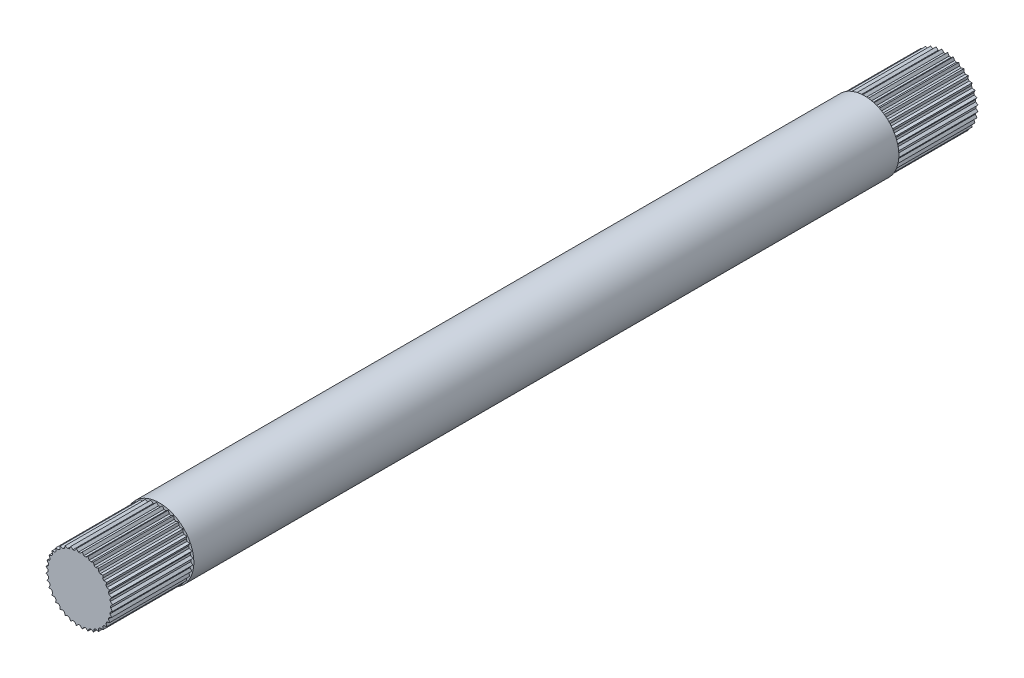
SolidWorks part; units mm, degrees
material "AISI 1015 Steel, Cold Drawn (SS)"
ref_plane "X-Y Datum" through (0, 0, 0) normal (0, 0, 1) x (1, 0, 0)
ref_plane "X-Z Datum" through (0, 0, 0) normal (0, 1, 0) x (1, 0, 0)
ref_plane "Y-Z Datum" through (0, 0, 0) normal (1, 0, 0) x (0, 0, -1)
sketch "Sketch9" plane through (0, 0, 0) normal (0, 1, 0) x (1, 0, 0)
  line L0 (16.002, 0) -> (0, 0)
  line L1 (0, 0) -> (0, -389.0916)
  line L2 (0, -389.0916) -> (-72.2493, -524.9728)
  dimension "D1" = 153.895
  dimension "D2" = 28
  dimension "D3" = 389.0916
  dimension "D5" = 16.002
sketch "Sketch5" plane through (0, 0, 0) normal (0, 1, 0) x (1, 0, 0)
  line L0 (7.9375, -262.0916) -> (7.9375, -22.1615)
  line L1 (7.9375, -22.1615) -> (9.525, -22.1615)
  line L2 (9.525, -22.1615) -> (9.525, -262.0916)
  line L3 (9.525, -262.0916) -> (7.9375, -262.0916)
  line L5 (16.002, 0) -> (0, 0) construction
  line L6 (0, 0) -> (0, -389.0916) construction
  line L7 (0, -389.0916) -> (9.525, -389.0916) construction
  line L8 (12.5602, -369.8416) -> (0, -369.8416) construction
  dimension "D1" = 1.5875
  dimension "D2" = 22.1615
  dimension "D3" = 7.9375
  dimension "D4" = 19.25
  dimension "D5" = 127
revolve "Revolve2" add sketch "Sketch5" angle 360 about L1
sketch "Sketch6" plane through (0, 0, 0) normal (0, 1, 0) x (1, 0, 0)
  circle A0 centre (0, -33.1635) radius 1.5875 construction
  circle A1 centre (0, -33.1635) radius 1.5875
sketch "Sketch7" plane through (0, 0, 0) normal (1, 0, 0) x (0, 0, -1)
  circle A2 centre (-39.196, 0) radius 1.5875
  circle A4 centre (-39.196, 0) radius 1.5875 construction
extrude "Cut-Extrude5" [suppressed] cut sketch "Sketch7" against normal through all both and the other way through all
extrude "Cut-Extrude6" [suppressed] cut sketch "Sketch6" against normal through all both and the other way through all
sketch "Sketch8" plane through (0, 0, 0) normal (0, 0, 1) x (1, 0, 0)
  line L0 (9.2357, -0.808) -> (8.6817, -0.254)
  line L1 (8.6817, -0.254) -> (8.6817, 0.254)
  line L2 (8.6817, 0.254) -> (9.2357, 0.808)
  line L3 (8.6817, 0) -> (0, 0) construction
  line L4 (8.9551, -2.3995) -> (8.5057, -1.7577)
  line L5 (8.5057, -1.7577) -> (8.5939, -1.2574)
  line L6 (8.5939, -1.2574) -> (9.2357, -0.808)
  line L7 (8.4024, -3.9181) -> (8.0713, -3.208)
  line L8 (8.0713, -3.208) -> (8.245, -2.7306)
  line L9 (8.245, -2.7306) -> (8.9551, -2.3995)
  line L10 (7.5944, -5.3176) -> (7.3916, -4.5608)
  line L11 (7.3916, -4.5608) -> (7.6456, -4.1209)
  line L12 (7.6456, -4.1209) -> (8.4024, -3.9181)
  line L13 (6.5556, -6.5556) -> (6.4873, -5.7751)
  line L14 (6.4873, -5.7751) -> (6.8138, -5.3859)
  line L15 (6.8138, -5.3859) -> (7.5944, -5.3176)
  line L16 (5.3176, -7.5944) -> (5.3859, -6.8138)
  line L17 (5.3859, -6.8138) -> (5.7751, -6.4873)
  line L18 (5.7751, -6.4873) -> (6.5556, -6.5556)
  line L19 (3.9181, -8.4024) -> (4.1209, -7.6456)
  line L20 (4.1209, -7.6456) -> (4.5608, -7.3916)
  line L21 (4.5608, -7.3916) -> (5.3176, -7.5944)
  line L22 (2.3995, -8.9551) -> (2.7306, -8.245)
  line L23 (2.7306, -8.245) -> (3.208, -8.0713)
  line L24 (3.208, -8.0713) -> (3.9181, -8.4024)
  line L25 (0.808, -9.2357) -> (1.2574, -8.5939)
  line L26 (1.2574, -8.5939) -> (1.7577, -8.5057)
  line L27 (1.7577, -8.5057) -> (2.3995, -8.9551)
  line L28 (-0.808, -9.2357) -> (-0.254, -8.6817)
  line L29 (-0.254, -8.6817) -> (0.254, -8.6817)
  line L30 (0.254, -8.6817) -> (0.808, -9.2357)
  line L31 (-2.3995, -8.9551) -> (-1.7577, -8.5057)
  line L32 (-1.7577, -8.5057) -> (-1.2574, -8.5939)
  line L33 (-1.2574, -8.5939) -> (-0.808, -9.2357)
  line L34 (-3.9181, -8.4024) -> (-3.208, -8.0713)
  line L35 (-3.208, -8.0713) -> (-2.7306, -8.245)
  line L36 (-2.7306, -8.245) -> (-2.3995, -8.9551)
  line L37 (-5.3176, -7.5944) -> (-4.5608, -7.3916)
  line L38 (-4.5608, -7.3916) -> (-4.1209, -7.6456)
  line L39 (-4.1209, -7.6456) -> (-3.9181, -8.4024)
  line L40 (-6.5556, -6.5556) -> (-5.7751, -6.4873)
  line L41 (-5.7751, -6.4873) -> (-5.3859, -6.8138)
  line L42 (-5.3859, -6.8138) -> (-5.3176, -7.5944)
  line L43 (-7.5944, -5.3176) -> (-6.8138, -5.3859)
  line L44 (-6.8138, -5.3859) -> (-6.4873, -5.7751)
  line L45 (-6.4873, -5.7751) -> (-6.5556, -6.5556)
  line L46 (-8.4024, -3.9181) -> (-7.6456, -4.1209)
  line L47 (-7.6456, -4.1209) -> (-7.3916, -4.5608)
  line L48 (-7.3916, -4.5608) -> (-7.5944, -5.3176)
  line L49 (-8.9551, -2.3995) -> (-8.245, -2.7306)
  line L50 (-8.245, -2.7306) -> (-8.0713, -3.208)
  line L51 (-8.0713, -3.208) -> (-8.4024, -3.9181)
  line L52 (-9.2357, -0.808) -> (-8.5939, -1.2574)
  line L53 (-8.5939, -1.2574) -> (-8.5057, -1.7577)
  line L54 (-8.5057, -1.7577) -> (-8.9551, -2.3995)
  line L55 (-9.2357, 0.808) -> (-8.6817, 0.254)
  line L56 (-8.6817, 0.254) -> (-8.6817, -0.254)
  line L57 (-8.6817, -0.254) -> (-9.2357, -0.808)
  line L58 (-8.9551, 2.3995) -> (-8.5057, 1.7577)
  line L59 (-8.5057, 1.7577) -> (-8.5939, 1.2574)
  line L60 (-8.5939, 1.2574) -> (-9.2357, 0.808)
  line L61 (-8.4024, 3.9181) -> (-8.0713, 3.208)
  line L62 (-8.0713, 3.208) -> (-8.245, 2.7306)
  line L63 (-8.245, 2.7306) -> (-8.9551, 2.3995)
  line L64 (-7.5944, 5.3176) -> (-7.3916, 4.5608)
  line L65 (-7.3916, 4.5608) -> (-7.6456, 4.1209)
  line L66 (-7.6456, 4.1209) -> (-8.4024, 3.9181)
  line L67 (-6.5556, 6.5556) -> (-6.4873, 5.7751)
  line L68 (-6.4873, 5.7751) -> (-6.8138, 5.3859)
  line L69 (-6.8138, 5.3859) -> (-7.5944, 5.3176)
  line L70 (-5.3176, 7.5944) -> (-5.3859, 6.8138)
  line L71 (-5.3859, 6.8138) -> (-5.7751, 6.4873)
  line L72 (-5.7751, 6.4873) -> (-6.5556, 6.5556)
  line L73 (-3.9181, 8.4024) -> (-4.1209, 7.6456)
  line L74 (-4.1209, 7.6456) -> (-4.5608, 7.3916)
  line L75 (-4.5608, 7.3916) -> (-5.3176, 7.5944)
  line L76 (-2.3995, 8.9551) -> (-2.7306, 8.245)
  line L77 (-2.7306, 8.245) -> (-3.208, 8.0713)
  line L78 (-3.208, 8.0713) -> (-3.9181, 8.4024)
  line L79 (-0.808, 9.2357) -> (-1.2574, 8.5939)
  line L80 (-1.2574, 8.5939) -> (-1.7577, 8.5057)
  line L81 (-1.7577, 8.5057) -> (-2.3995, 8.9551)
  line L82 (0.808, 9.2357) -> (0.254, 8.6817)
  line L83 (0.254, 8.6817) -> (-0.254, 8.6817)
  line L84 (-0.254, 8.6817) -> (-0.808, 9.2357)
  line L85 (2.3995, 8.9551) -> (1.7577, 8.5057)
  line L86 (1.7577, 8.5057) -> (1.2574, 8.5939)
  line L87 (1.2574, 8.5939) -> (0.808, 9.2357)
  line L88 (3.9181, 8.4024) -> (3.208, 8.0713)
  line L89 (3.208, 8.0713) -> (2.7306, 8.245)
  line L90 (2.7306, 8.245) -> (2.3995, 8.9551)
  line L91 (5.3176, 7.5944) -> (4.5608, 7.3916)
  line L92 (4.5608, 7.3916) -> (4.1209, 7.6456)
  line L93 (4.1209, 7.6456) -> (3.9181, 8.4024)
  line L94 (6.5556, 6.5556) -> (5.7751, 6.4873)
  line L95 (5.7751, 6.4873) -> (5.3859, 6.8138)
  line L96 (5.3859, 6.8138) -> (5.3176, 7.5944)
  line L97 (7.5944, 5.3176) -> (6.8138, 5.3859)
  line L98 (6.8138, 5.3859) -> (6.4873, 5.7751)
  line L99 (6.4873, 5.7751) -> (6.5556, 6.5556)
  line L100 (8.4024, 3.9181) -> (7.6456, 4.1209)
  line L101 (7.6456, 4.1209) -> (7.3916, 4.5608)
  line L102 (7.3916, 4.5608) -> (7.5944, 5.3176)
  line L103 (8.9551, 2.3995) -> (8.245, 2.7306)
  line L104 (8.245, 2.7306) -> (8.0713, 3.208)
  line L105 (8.0713, 3.208) -> (8.4024, 3.9181)
  line L106 (9.2357, 0.808) -> (8.5939, 1.2574)
  line L107 (8.5939, 1.2574) -> (8.5057, 1.7577)
  line L108 (8.5057, 1.7577) -> (8.9551, 2.3995)
  circle A0 centre (0, 0) radius 12.7
  circle A1 centre (0, 0) radius 9.271 construction
  circle A2 centre (0, 0) radius 8.6854 construction
  point P153 (0, 0)
  dimension "D1" = 25.4
  dimension "D4" = 18.542
  dimension "D6" = 17.3708
  dimension "D2" = 0.508
  dimension "D3" = 135
  dimension "D5" = 36
extrude "Cut-Extrude7" cut sketch "Sketch8" against normal blind 22.225 from surface at 262.0916 starting at face at (-9.525, 0, 262.0916)
ref_plane "Plane1" through (0, 0, 47.5615) normal (0, 0, -1) x (-1, 0, 0)
sketch "Sketch10" plane through (0, 0, 47.5615) normal (0, 0, -1) x (-1, 0, 0)
  circle A0 centre (0, 0) radius 7.9375
  dimension "D1" = 15.875
extrude "Boss-Extrude1" add sketch "Sketch10" against normal up to surface (214.5301 mm away) up to face at (-7.9375, 0, 262.0916)
sketch "Sketch11" plane through (0, 0, 22.1615) normal (0, 0, -1) x (-1, 0, 0)
  line L0 (0, 9.525) -> (13.3548, 9.525) construction
  line L1 (0, 9.525) -> (0, 15.4312) construction
  line L2 (-9.525, 0) -> (-9.525, 9.1744) construction
  line L3 (-9.525, 0) -> (-16.674, 0) construction
  circle A0 centre (0, 0) radius 9.525 construction
  point P0 (0, 9.525)
  point P1 (-9.525, 0)
sketch "Sketch12" plane through (0, 0, 0) normal (0, 0, 1) x (1, 0, 0)
  line L0 (9.2357, -0.808) -> (8.6817, -0.254)
  line L1 (8.6817, -0.254) -> (8.6817, 0.254)
  line L2 (8.6817, 0.254) -> (9.2357, 0.808)
  line L3 (8.6817, 0) -> (0, 0) construction
  line L4 (8.9551, -2.3995) -> (8.5057, -1.7577)
  line L5 (8.5057, -1.7577) -> (8.5939, -1.2574)
  line L6 (8.5939, -1.2574) -> (9.2357, -0.808)
  line L7 (8.4024, -3.9181) -> (8.0713, -3.208)
  line L8 (8.0713, -3.208) -> (8.245, -2.7306)
  line L9 (8.245, -2.7306) -> (8.9551, -2.3995)
  line L10 (7.5944, -5.3176) -> (7.3916, -4.5608)
  line L11 (7.3916, -4.5608) -> (7.6456, -4.1209)
  line L12 (7.6456, -4.1209) -> (8.4024, -3.9181)
  line L13 (6.5556, -6.5556) -> (6.4873, -5.7751)
  line L14 (6.4873, -5.7751) -> (6.8138, -5.3859)
  line L15 (6.8138, -5.3859) -> (7.5944, -5.3176)
  line L16 (5.3176, -7.5944) -> (5.3859, -6.8138)
  line L17 (5.3859, -6.8138) -> (5.7751, -6.4873)
  line L18 (5.7751, -6.4873) -> (6.5556, -6.5556)
  line L19 (3.9181, -8.4024) -> (4.1209, -7.6456)
  line L20 (4.1209, -7.6456) -> (4.5608, -7.3916)
  line L21 (4.5608, -7.3916) -> (5.3176, -7.5944)
  line L22 (2.3995, -8.9551) -> (2.7306, -8.245)
  line L23 (2.7306, -8.245) -> (3.208, -8.0713)
  line L24 (3.208, -8.0713) -> (3.9181, -8.4024)
  line L25 (0.808, -9.2357) -> (1.2574, -8.5939)
  line L26 (1.2574, -8.5939) -> (1.7577, -8.5057)
  line L27 (1.7577, -8.5057) -> (2.3995, -8.9551)
  line L28 (-0.808, -9.2357) -> (-0.254, -8.6817)
  line L29 (-0.254, -8.6817) -> (0.254, -8.6817)
  line L30 (0.254, -8.6817) -> (0.808, -9.2357)
  line L31 (-2.3995, -8.9551) -> (-1.7577, -8.5057)
  line L32 (-1.7577, -8.5057) -> (-1.2574, -8.5939)
  line L33 (-1.2574, -8.5939) -> (-0.808, -9.2357)
  line L34 (-3.9181, -8.4024) -> (-3.208, -8.0713)
  line L35 (-3.208, -8.0713) -> (-2.7306, -8.245)
  line L36 (-2.7306, -8.245) -> (-2.3995, -8.9551)
  line L37 (-5.3176, -7.5944) -> (-4.5608, -7.3916)
  line L38 (-4.5608, -7.3916) -> (-4.1209, -7.6456)
  line L39 (-4.1209, -7.6456) -> (-3.9181, -8.4024)
  line L40 (-6.5556, -6.5556) -> (-5.7751, -6.4873)
  line L41 (-5.7751, -6.4873) -> (-5.3859, -6.8138)
  line L42 (-5.3859, -6.8138) -> (-5.3176, -7.5944)
  line L43 (-7.5944, -5.3176) -> (-6.8138, -5.3859)
  line L44 (-6.8138, -5.3859) -> (-6.4873, -5.7751)
  line L45 (-6.4873, -5.7751) -> (-6.5556, -6.5556)
  line L46 (-8.4024, -3.9181) -> (-7.6456, -4.1209)
  line L47 (-7.6456, -4.1209) -> (-7.3916, -4.5608)
  line L48 (-7.3916, -4.5608) -> (-7.5944, -5.3176)
  line L49 (-8.9551, -2.3995) -> (-8.245, -2.7306)
  line L50 (-8.245, -2.7306) -> (-8.0713, -3.208)
  line L51 (-8.0713, -3.208) -> (-8.4024, -3.9181)
  line L52 (-9.2357, -0.808) -> (-8.5939, -1.2574)
  line L53 (-8.5939, -1.2574) -> (-8.5057, -1.7577)
  line L54 (-8.5057, -1.7577) -> (-8.9551, -2.3995)
  line L55 (-9.2357, 0.808) -> (-8.6817, 0.254)
  line L56 (-8.6817, 0.254) -> (-8.6817, -0.254)
  line L57 (-8.6817, -0.254) -> (-9.2357, -0.808)
  line L58 (-8.9551, 2.3995) -> (-8.5057, 1.7577)
  line L59 (-8.5057, 1.7577) -> (-8.5939, 1.2574)
  line L60 (-8.5939, 1.2574) -> (-9.2357, 0.808)
  line L61 (-8.4024, 3.9181) -> (-8.0713, 3.208)
  line L62 (-8.0713, 3.208) -> (-8.245, 2.7306)
  line L63 (-8.245, 2.7306) -> (-8.9551, 2.3995)
  line L64 (-7.5944, 5.3176) -> (-7.3916, 4.5608)
  line L65 (-7.3916, 4.5608) -> (-7.6456, 4.1209)
  line L66 (-7.6456, 4.1209) -> (-8.4024, 3.9181)
  line L67 (-6.5556, 6.5556) -> (-6.4873, 5.7751)
  line L68 (-6.4873, 5.7751) -> (-6.8138, 5.3859)
  line L69 (-6.8138, 5.3859) -> (-7.5944, 5.3176)
  line L70 (-5.3176, 7.5944) -> (-5.3859, 6.8138)
  line L71 (-5.3859, 6.8138) -> (-5.7751, 6.4873)
  line L72 (-5.7751, 6.4873) -> (-6.5556, 6.5556)
  line L73 (-3.9181, 8.4024) -> (-4.1209, 7.6456)
  line L74 (-4.1209, 7.6456) -> (-4.5608, 7.3916)
  line L75 (-4.5608, 7.3916) -> (-5.3176, 7.5944)
  line L76 (-2.3995, 8.9551) -> (-2.7306, 8.245)
  line L77 (-2.7306, 8.245) -> (-3.208, 8.0713)
  line L78 (-3.208, 8.0713) -> (-3.9181, 8.4024)
  line L79 (-0.808, 9.2357) -> (-1.2574, 8.5939)
  line L80 (-1.2574, 8.5939) -> (-1.7577, 8.5057)
  line L81 (-1.7577, 8.5057) -> (-2.3995, 8.9551)
  line L82 (0.808, 9.2357) -> (0.254, 8.6817)
  line L83 (0.254, 8.6817) -> (-0.254, 8.6817)
  line L84 (-0.254, 8.6817) -> (-0.808, 9.2357)
  line L85 (2.3995, 8.9551) -> (1.7577, 8.5057)
  line L86 (1.7577, 8.5057) -> (1.2574, 8.5939)
  line L87 (1.2574, 8.5939) -> (0.808, 9.2357)
  line L88 (3.9181, 8.4024) -> (3.208, 8.0713)
  line L89 (3.208, 8.0713) -> (2.7306, 8.245)
  line L90 (2.7306, 8.245) -> (2.3995, 8.9551)
  line L91 (5.3176, 7.5944) -> (4.5608, 7.3916)
  line L92 (4.5608, 7.3916) -> (4.1209, 7.6456)
  line L93 (4.1209, 7.6456) -> (3.9181, 8.4024)
  line L94 (6.5556, 6.5556) -> (5.7751, 6.4873)
  line L95 (5.7751, 6.4873) -> (5.3859, 6.8138)
  line L96 (5.3859, 6.8138) -> (5.3176, 7.5944)
  line L97 (7.5944, 5.3176) -> (6.8138, 5.3859)
  line L98 (6.8138, 5.3859) -> (6.4873, 5.7751)
  line L99 (6.4873, 5.7751) -> (6.5556, 6.5556)
  line L100 (8.4024, 3.9181) -> (7.6456, 4.1209)
  line L101 (7.6456, 4.1209) -> (7.3916, 4.5608)
  line L102 (7.3916, 4.5608) -> (7.5944, 5.3176)
  line L103 (8.9551, 2.3995) -> (8.245, 2.7306)
  line L104 (8.245, 2.7306) -> (8.0713, 3.208)
  line L105 (8.0713, 3.208) -> (8.4024, 3.9181)
  line L106 (9.2357, 0.808) -> (8.5939, 1.2574)
  line L107 (8.5939, 1.2574) -> (8.5057, 1.7577)
  line L108 (8.5057, 1.7577) -> (8.9551, 2.3995)
  circle A0 centre (0, 0) radius 12.7
  circle A1 centre (0, 0) radius 9.271 construction
  circle A2 centre (0, 0) radius 8.6854 construction
  point P153 (0, 0)
  dimension "D1" = 25.4
  dimension "D4" = 18.542
  dimension "D6" = 17.3708
  dimension "D2" = 0.508
  dimension "D3" = 135
  dimension "D5" = 36
extrude "Cut-Extrude8" cut sketch "Sketch12" along normal blind 22.225 from surface at 22.1615 starting at face at (-7.9375, 0, 22.1615)
